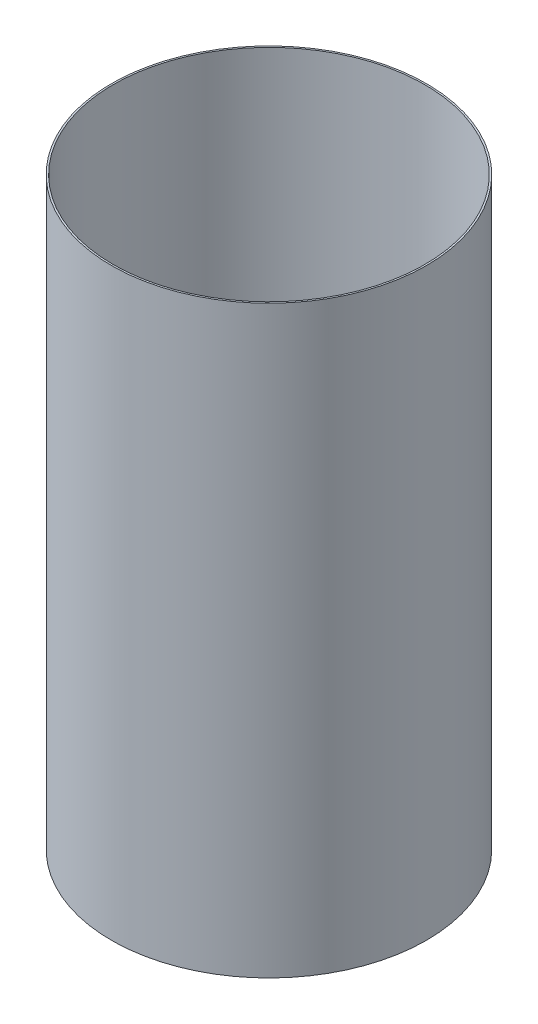
SolidWorks part; units mm, degrees
material "Glass"
ref_plane "Front Plane" through (0, 0, 0) normal (0, 0, 1) x (1, 0, 0)
ref_plane "Top Plane" through (0, 0, 0) normal (0, 1, 0) x (1, 0, 0)
ref_plane "Right Plane" through (0, 0, 0) normal (1, 0, 0) x (0, 0, -1)
sketch "Sketch1" plane through (0, 0, 0) normal (0, 1, 0) x (1, 0, 0)
  circle A0 centre (0, 0) radius 50.8
  dimension "D1" = 101.6
extrude "Extrude-Thin1" add sketch "Sketch1" along normal blind 190.5 thin
